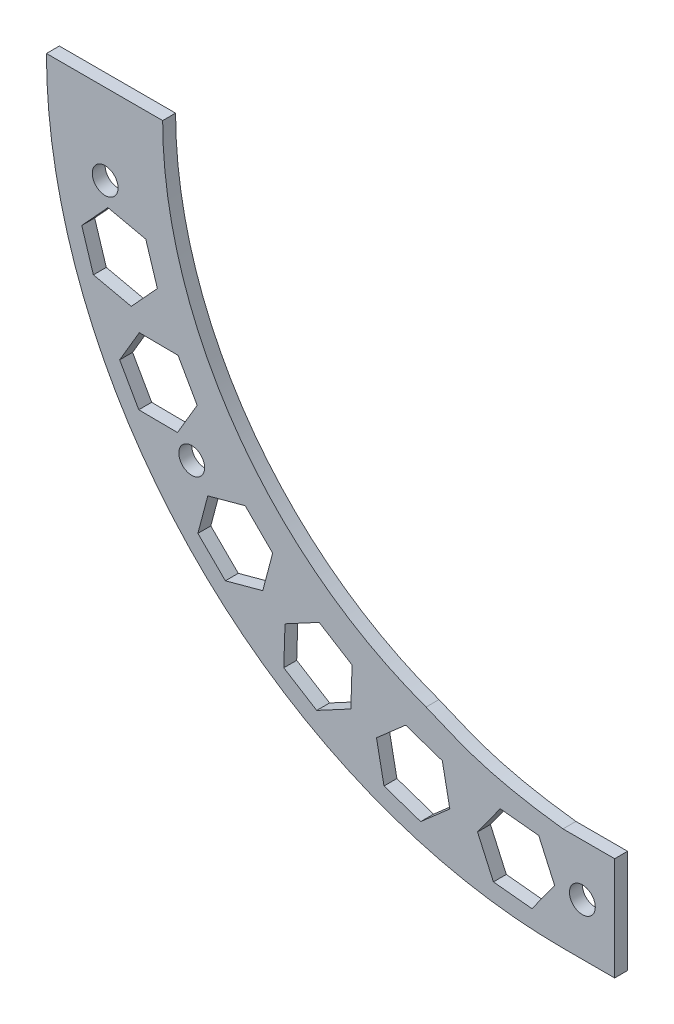
SolidWorks part; units mm, degrees
material "6061-T6 (SS)"
ref_plane "Front Plane" through (0, 0, 0) normal (0, 0, 1) x (1, 0, 0)
ref_plane "Top Plane" through (0, 0, 0) normal (0, 1, 0) x (1, 0, 0)
ref_plane "Right Plane" through (0, 0, 0) normal (1, 0, 0) x (0, 0, -1)
sketch "Layout" plane through (0, 0, 0) normal (0, 0, 1) x (1, 0, 0)
  line L0 (0, 0) -> (-76.2, 0) construction
  line L1 (-76.2, 0) -> (-203.2, 0) construction
  dimension "D1" = 76.2
  dimension "D2" = 127
sketch "Sketch1" plane through (0, 0, 0) normal (0, 0, 1) x (1, 0, 0)
  line L0 (0, 0) -> (-203.2, 0) construction
  line L1 (0, 0) -> (0, -203.2) construction
  line L2 (0, -203.2) -> (25.4, -203.2)
  line L3 (0, -254) -> (25.4, -254)
  line L4 (-254, 0) -> (-203.2, 0)
  line L5 (25.4, -203.2) -> (25.4, -254)
  arc A0 (-203.2, 0) -> (0, -203.2) centre (0, 0) ccw
  arc A1 (-254, 0) -> (0, -254) centre (0, 0) ccw
  dimension "D1" = 50.8
  dimension "D2" = 25.4
  dimension "D3" = 203.2
extrude "Boss-Extrude1" add sketch "Sketch1" along normal blind 6.35
sketch "Mid_Point_Sk" plane through (0, 0, 0) normal (0, 1, 0) x (1, 0, 0)
  line L0 (-254, 0) -> (-203.2, -6.35) construction
  line L1 (-254, -6.35) -> (-203.2, 0) construction
ref_point "Mid_Point"
ref_plane "Mid_Plane" through (0, 0, 3.175) normal (0, 0, 1) x (1, 0, 0)
sketch "Sketch2" plane through (0, 0, 6.35) normal (0, 0, 1) x (1, 0, 0)
  line L0 (0, 0) -> (-229.3095, 0) construction
  line L1 (0, 0) -> (-222.5647, -39.2442) construction
  line L2 (0, 0) -> (-173.1246, -145.2688) construction
  arc A0 (-222.5647, -39.2442) -> (-173.1246, -145.2688) centre (0, 0) ccw construction
  arc A1 (-222.5647, -39.2442) -> (-173.1246, -145.2688) centre (0, 0) ccw construction
  arc A2 (-228.8182, -40.3468) -> (-177.989, -149.3505) centre (0, 0) ccw
  arc A3 (-216.3112, -38.1415) -> (-168.2602, -141.1871) centre (0, 0) ccw
  arc A4 (-216.3112, -38.1415) -> (-228.8182, -40.3468) centre (-222.5647, -39.2442) ccw
  arc A5 (-177.989, -149.3505) -> (-168.2602, -141.1871) centre (-173.1246, -145.2688) ccw
  point P5 (-204.8238, -95.5109)
  dimension "D1" = 30
  dimension "D3" = 12.7
  dimension "D2" = 10
sketch "Sketch3" plane through (0, 0, 6.35) normal (0, 0, 1) x (1, 0, 0)
  line L0 (0, 0) -> (-225.1271, -39.696) construction
  line L1 (0, 0) -> (-182.5681, -137.5749) construction
  line L2 (-203.2, 0) -> (-254, 0) construction
  circle A1 centre (-182.5681, -137.5749) radius 6.35
  circle A3 centre (-225.1271, -39.696) radius 6.35
  dimension "D1" = 228.6
  dimension "D2" = 27
  dimension "D3" = 10
extrude "Cut-Extrude1" cut sketch "Sketch3" against normal up to next
sketch "Sketch4" plane through (0, 0, 6.35) normal (0, 0, 1) x (1, 0, 0)
  line L0 (0, -203.2) -> (0, -228.6) construction
  line L1 (0, -228.6) -> (9.525, -228.6) construction
  circle A1 centre (9.525, -228.6) radius 6.35
  dimension "D1" = 25.4
  dimension "D2" = 9.525
extrude "Cut-Extrude2" cut sketch "Sketch4" against normal up to next
sketch "Sketch5" plane through (0, 0, 6.35) normal (0, 0, 1) x (1, 0, 0)
  line L0 (0, 0) -> (-67.3267, -184.9785) construction
  line L2 (0, 0) -> (-196.85, 0) construction
  line L3 (-196.85, 0) -> (-203.2, 0)
  arc A0 (-67.3267, -184.9785) -> (-196.85, 0) centre (0, 0) cw
  arc A1 (-203.2, 0) -> (0, -203.2) centre (0, 0) ccw construction
  arc A2 (-203.2, 0) -> (0, -203.2) centre (0, 0) ccw
  spline S0 degree 3 poles (0, -203.2) (-42.7386, -198.0277) (-55.3777, -189.3302) (-67.3267, -184.9785) knots 0 0 0 0 1 1 1 1
  dimension "D1" = 70
  dimension "D2" = 196.85
extrude "Boss-Extrude2" add sketch "Sketch5" against normal up to surface (6.35 mm away) up to face at (15.875, -228.6, 0)
sketch "Sketch7" plane through (0, 0, 6.35) normal (0, 0, 1) x (1, 0, 0)
  line L0 (-196.85, 0) -> (-254, 0) construction
  line L1 (25.4, -203.2) -> (0, -203.2) construction
  line L2 (25.4, -254) -> (25.4, -203.2) construction
  line L3 (0, -254) -> (25.4, -254) construction
  line L4 (-196.85, 0) -> (-224.155, 0)
  line L5 (25.4, -203.2) -> (0, -203.2)
  line L6 (25.4, -254) -> (25.4, -231.14)
  line L7 (0, -254) -> (25.4, -254)
  line L8 (-225.425, 0) -> (-225.425, 6.35) construction
  line L9 (-224.155, 0) -> (-224.155, 6.35)
  line L10 (-226.695, 0) -> (-226.695, 6.35)
  line L11 (-226.695, 0) -> (-254, 0)
  line L12 (-225.425, 0) -> (-225.425, 6.35) construction
  line L13 (25.4, -228.6) -> (31.75, -228.6) construction
  line L14 (25.4, -231.14) -> (31.75, -231.14)
  line L15 (25.4, -226.06) -> (31.75, -226.06)
  line L16 (25.4, -226.06) -> (25.4, -203.2)
  line L17 (-221.0637, -125.0872) -> (-226.5903, -128.2144) construction
  line L18 (-222.3036, -122.8704) -> (-227.8412, -126.0038)
  line L19 (-219.8018, -127.2916) -> (-225.3395, -130.4251)
  line L20 (-222.3146, -122.8766) -> (-227.8412, -126.0038) construction
  line L21 (-219.8129, -127.2979) -> (-225.3395, -130.4251) construction
  line L22 (-65.7713, -245.3368) -> (-67.4156, -251.4702) construction
  line L23 (-68.2214, -244.6668) -> (-69.869, -250.8125)
  line L24 (-63.3147, -245.9822) -> (-64.9623, -252.1279)
  line L25 (-68.2247, -244.6791) -> (-69.869, -250.8125) construction
  line L26 (-63.318, -245.9945) -> (-64.9623, -252.1279) construction
  arc A0 (-196.85, 0) -> (-67.3267, -184.9785) centre (0, 0) ccw construction
  arc A1 (-254, 0) -> (0, -254) centre (0, 0) ccw construction
  arc A2 (-196.85, 0) -> (-67.3267, -184.9785) centre (0, 0) ccw
  arc A3 (-254, 0) -> (-222.3036, -122.8704) centre (0, 0) ccw
  arc A4 (-219.8018, -127.2916) -> (-68.2214, -244.6668) centre (0, 0) ccw
  arc A5 (-63.3147, -245.9822) -> (0, -254) centre (0, 0) ccw
  spline S0 degree 3 poles (1981.8646, 56.2486) (-1874.2993, -629.1178) (1692.2753, 387.4221) (-1965.7391, -814.2312) knots -2.993489 -2.993489 -2.993489 -2.993489 4.933194 4.933194 4.933194 4.933194 only from (0, -203.2) to (-67.3267, -184.9785) construction
  spline S1 degree 3 poles (0, -203.2) (-42.7386, -198.0277) (-55.3777, -189.3302) (-67.3267, -184.9785) knots 0 0 0 0 1 1 1 1
  dimension "D3" = 6.35
  dimension "D4" = 2.54
  dimension "D6" = 2.54
  dimension "D8" = 2.54
  dimension "D1" = 1.27
  dimension "D2" = 1.27
  dimension "D5" = 2.54
  dimension "D7" = 2.54
  dimension "D9" = 2.54
sketch "Sketch8" plane through (0, 0, 6.35) normal (0, 0, 1) x (1, 0, 0)
  line L0 (-147.6288, -175.5751) -> (-136.6921, -184.2176) construction
  line L1 (-104.3155, -204.3016) -> (-91.7139, -210.2604) construction
  line L2 (-55.6472, -222.5405) -> (-42.0276, -225.5095) construction
  line L3 (-174.6532, -148.7182) -> (-182.5681, -137.5749) construction
  line L4 (-4.1222, -229.3553) -> (9.525, -228.6) construction
  line L5 (-212.3127, -86.8572) -> (-208.3203, -96.0392) construction
  line L6 (-189.5507, -129.1951) -> (-182.5681, -137.5749) construction
  line L7 (-223.7606, -50.5178) -> (-225.1271, -39.696) construction
  circle A0 centre (0, 0) radius 228.6 construction
  line B0 (0, 0) -> (-184.5786, -104.4897) construction
  line B1 (-189.5507, -129.1951) -> (-179.8862, -112.7787)
  line B2 (-179.8862, -112.7787) -> (-189.271, -96.2007)
  line B3 (-189.271, -96.2007) -> (-208.3203, -96.0392)
  line B4 (-208.3203, -96.0392) -> (-217.9848, -112.4556)
  line B5 (-217.9848, -112.4556) -> (-208.6001, -129.0336)
  line B6 (-208.6001, -129.0336) -> (-189.5507, -129.1951)
  circle B7 centre (-198.9355, -112.6172) radius 16.4978 construction
  line B8 (0, 0) -> (-202.3012, -63.7304) construction
  line B9 (-212.3127, -86.8572) -> (-199.4392, -72.8153)
  line B10 (-199.4392, -72.8153) -> (-205.1632, -54.6455)
  line B11 (-205.1632, -54.6455) -> (-223.7606, -50.5178)
  line B12 (-223.7606, -50.5178) -> (-236.6341, -64.5597)
  line B13 (-236.6341, -64.5597) -> (-230.9101, -82.7295)
  line B14 (-230.9101, -82.7295) -> (-212.3127, -86.8572)
  line B15 (0, 0) -> (-149.5117, -150.4447) construction
  line B16 (-147.6288, -175.5751) -> (-142.7556, -157.1589)
  line B17 (-142.7556, -157.1589) -> (-156.2678, -143.7305)
  line B18 (-156.2678, -143.7305) -> (-174.6532, -148.7182)
  line B19 (-174.6532, -148.7182) -> (-179.5265, -167.1343)
  line B20 (-179.5265, -167.1343) -> (-166.0143, -180.5628)
  line B21 (-166.0143, -180.5628) -> (-147.6288, -175.5751)
  line B22 (0, 0) -> (-111.8072, -180.2401) construction
  line B23 (-104.3155, -204.3016) -> (-103.713, -185.2611)
  line B24 (-103.713, -185.2611) -> (-119.9013, -175.2192)
  line B25 (-119.9013, -175.2192) -> (-136.6921, -184.2176)
  line B26 (-136.6921, -184.2176) -> (-137.2945, -203.2581)
  line B27 (-137.2945, -203.2581) -> (-121.1062, -213.3001)
  line B28 (-121.1062, -213.3001) -> (-104.3155, -204.3016)
  line B29 (0, 0) -> (-68.3631, -200.7831) construction
  line B30 (-55.6472, -222.5405) -> (-59.3464, -203.8531)
  line B31 (-59.3464, -203.8531) -> (-77.3798, -197.713)
  line B32 (-77.3798, -197.713) -> (-91.7139, -210.2604)
  line B33 (-91.7139, -210.2604) -> (-88.0146, -228.9477)
  line B34 (-88.0146, -228.9477) -> (-69.9813, -235.0878)
  line B35 (-69.9813, -235.0878) -> (-55.6472, -222.5405)
  line B36 (0, 0) -> (-21.4097, -211.0189) construction
  line B37 (-4.1222, -229.3553) -> (-11.9333, -211.9804)
  line B38 (-11.9333, -211.9804) -> (-30.886, -210.0574)
  line B39 (-30.886, -210.0574) -> (-42.0276, -225.5095)
  line B40 (-42.0276, -225.5095) -> (-34.2166, -242.8845)
  line B41 (-34.2166, -242.8845) -> (-15.2639, -244.8074)
  line B42 (-15.2639, -244.8074) -> (-4.1222, -229.3553)
sketch_block_instance "Block1-1"
sketch_block "Block1"
sketch_block_instance "Block1-4"
sketch_block_instance "Block1-5"
sketch_block_instance "Block1-6"
sketch_block_instance "Block1-7"
sketch_block_instance "Block1-8"
extrude "Cut-Extrude4" cut sketch "Sketch8" against normal through all
